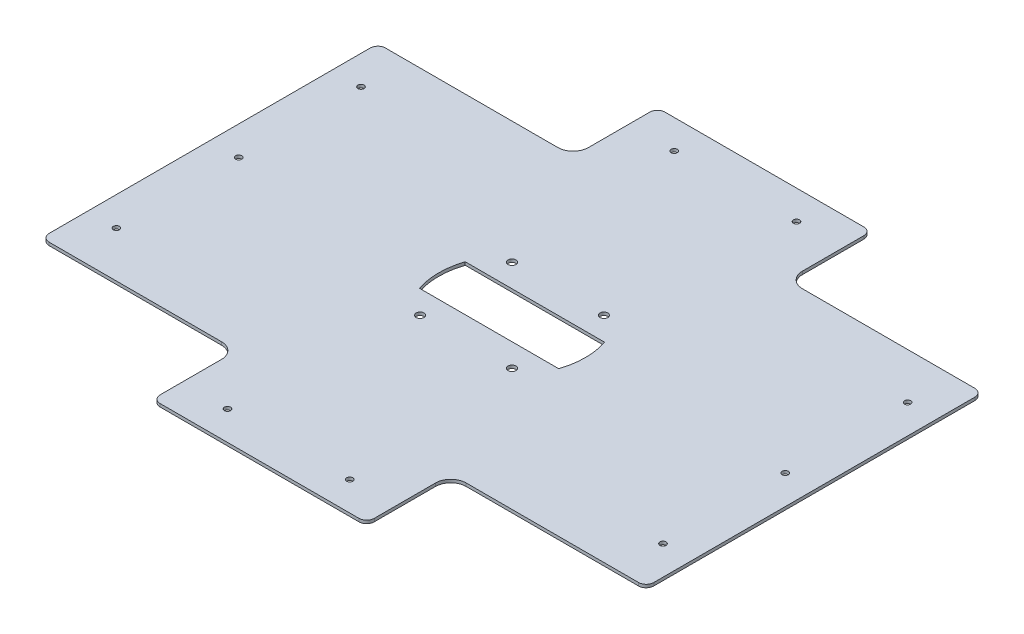
SolidWorks part; units mm, degrees
material "1060 Сплав"
ref_plane "Спереди" through (0, 0, 0) normal (0, 0, 1) x (1, 0, 0)
ref_plane "Сверху" through (0, 0, 0) normal (0, 1, 0) x (1, 0, 0)
ref_plane "Справа" through (0, 0, 0) normal (1, 0, 0) x (0, 0, -1)
sketch "Эскиз1" plane through (0, 0, 0) normal (0, 1, 0) x (1, 0, 0)
  line L1 (-65, -165.1043) -> (65, -165.1043)
  line L2 (-197.7687, -105) -> (-197.7687, 105)
  line L3 (-65, 165.1043) -> (65, 165.1043)
  line L4 (197.7687, -105) -> (197.7687, 105)
  line L18 (-284.5497, 0) -> (284.3305, 0) construction
  line L39 (-70, 120) -> (-70, 160.1043)
  line L40 (0, 262.7398) -> (0, -186.5795) construction
  line L41 (-192.7687, 110) -> (-80, 110)
  line L43 (-192.7687, -110) -> (-80, -110)
  line L44 (-70, -120) -> (-70, -160.1043)
  line L45 (70, 120) -> (70, 160.1043)
  line L46 (192.7687, 110) -> (80, 110)
  line L47 (192.7687, -110) -> (80, -110)
  line L48 (70, -120) -> (70, -160.1043)
  line L54 (160.9018, -110) -> (134.9018, -110)
  line L60 (160.9018, 110) -> (134.9018, 110)
  arc A0 (70, -120) -> (80, -110) centre (80, -120) cw
  arc A1 (70, 120) -> (80, 110) centre (80, 120) ccw
  arc A2 (-80, -110) -> (-70, -120) centre (-80, -120) cw
  arc A3 (-70, 120) -> (-80, 110) centre (-80, 120) cw
  arc A4 (192.7687, -110) -> (197.7687, -105) centre (192.7687, -105) ccw
  arc A5 (70, -160.1043) -> (65, -165.1043) centre (65, -160.1043) cw
  arc A6 (-70, -160.1043) -> (-65, -165.1043) centre (-65, -160.1043) ccw
  arc A7 (-192.7687, -110) -> (-197.7687, -105) centre (-192.7687, -105) cw
  arc A8 (-192.7687, 110) -> (-197.7687, 105) centre (-192.7687, 105) ccw
  arc A9 (197.7687, 105) -> (192.7687, 110) centre (192.7687, 105) ccw
  arc A10 (70, 160.1043) -> (65, 165.1043) centre (65, 160.1043) ccw
  arc A11 (-70, 160.1043) -> (-65, 165.1043) centre (-65, 160.1043) cw
  circle A22 centre (178.7687, 0) radius 2
  circle A23 centre (178.7687, 80) radius 2
  circle A24 centre (178.7687, -80) radius 2
  circle A25 centre (-178.7687, -80) radius 2
  circle A26 centre (-178.7687, 0) radius 2
  circle A27 centre (-178.7687, 80) radius 2
  circle A28 centre (40, 146.1043) radius 2
  circle A29 centre (-40, 146.1043) radius 2
  circle A30 centre (-40, -146.1043) radius 2
  circle A31 centre (40, -146.1043) radius 2
  point P0 (0, 0)
  point P3 (70, -110)
  point P8 (197.7687, 0)
  point P18 (-147.9018, 110)
  point P46 (70, 110)
  point P52 (-70, -110)
  point P55 (-70, 110)
  point P56 (-147.9018, 0)
  point P77 (197.7687, -110)
  point P80 (70, -165.1043)
  point P83 (-70, -165.1043)
  point P86 (-197.7687, -110)
  point P89 (-197.7687, 110)
  point P92 (197.7687, 110)
  point P95 (70, 165.1043)
  point P98 (-70, 165.1043)
  dimension "D2" = 4
  dimension "D6" = 10
  dimension "D11" = 40
  dimension "D12" = 330.2086
  dimension "D4" = 5
  dimension "D1" = 4
  dimension "D8" = 4
  dimension "D3" = 19
  dimension "D5" = 80
  dimension "D7" = 19
  dimension "D9" = 140
  dimension "D10" = 19
  dimension "D13" = 395.5373
sketch "Эскиз2" plane through (0, 0, 0) normal (0, 1, 0) x (1, 0, 0)
  line L0 (-162.9105, 114) -> (-136.9105, 114)
  line L1 (-162.9105, 114) -> (-162.9105, 0)
  line L2 (-162.9105, 0) -> (-136.9105, 0)
  line L3 (-136.9105, 114) -> (-136.9105, 0)
  line L4 (-149.9105, -192.6295) -> (-149.9105, 209.9923) construction
  line L5 (-162.9105, 0) -> (-136.9105, 0)
  line L6 (-162.9105, 0) -> (-162.9105, -114)
  line L7 (-162.9105, -114) -> (-136.9105, -114)
  line L8 (-136.9105, 0) -> (-136.9105, -114)
  line L9 (-99.9105, -123.5568) -> (-199.9105, -123.5568)
  line L10 (-99.9105, 163.4996) -> (-199.9105, 163.4996)
  line L11 (-99.9105, 163.4996) -> (-99.9105, 123.4996)
  line L12 (-99.9105, 123.4996) -> (-199.9105, 123.4996)
  line L13 (-199.9105, 163.4996) -> (-199.9105, 123.4996)
  line L14 (-199.9105, -163.5568) -> (-199.9105, -123.5568)
  line L15 (-99.9105, -163.5568) -> (-199.9105, -163.5568)
  line L16 (-99.9105, -163.5568) -> (-99.9105, -123.5568)
  line L17 (-284.5497, 0) -> (284.3305, 0) construction
  point P11 (-149.9105, 0)
  point P12 (-149.9105, 0)
sketch "Эскиз3" plane through (0, 0, 0) normal (0, 1, 0) x (1, 0, 0)
  line L0 (-89.8176, -177.9027) -> (70.2405, -177.9027)
  line L1 (-209.7886, -106.9112) -> (-209.7886, 106.8353)
  line L2 (-80.029, 172.0973) -> (50.2405, 172.0973)
  line L3 (170.2114, -106.9112) -> (170.2114, 103.9123)
  line L4 (-87.1938, 124.0033) -> (-87.1938, 164.9326)
  line L5 (-202.6239, 114) -> (-97.1971, 114)
  line L6 (-202.6239, -114.076) -> (-106.9857, -114.076)
  line L7 (-96.9823, -124.0793) -> (-96.9823, -170.738)
  line L8 (57.4052, 121.0803) -> (57.4052, 164.9326)
  line L9 (163.0467, 111.077) -> (67.4085, 111.077)
  line L10 (163.0467, -114.076) -> (87.4085, -114.076)
  line L11 (77.4052, -124.0793) -> (77.4052, -170.738)
  line L13 (-162.9105, 114) -> (-136.9105, 114) construction
  arc A0 (77.4052, -124.0793) -> (87.4085, -114.076) centre (87.4085, -124.0793) cw
  arc A1 (57.4052, 121.0803) -> (67.4085, 111.077) centre (67.4085, 121.0803) ccw
  arc A2 (-106.9857, -114.076) -> (-96.9823, -124.0793) centre (-106.9857, -124.0793) cw
  arc A3 (-87.1938, 124.0033) -> (-97.1971, 114) centre (-97.1971, 124.0033) cw
  arc A4 (-80.029, 172.0973) -> (-87.1938, 164.9326) centre (-80.029, 164.9326) ccw
  arc A5 (50.2405, 172.0973) -> (57.4052, 164.9326) centre (50.2405, 164.9326) cw
  arc A6 (170.2114, 103.9123) -> (163.0467, 111.077) centre (163.0467, 103.9123) ccw
  arc A7 (170.2114, -106.9112) -> (163.0467, -114.076) centre (163.0467, -106.9112) cw
  arc A8 (70.2405, -177.9027) -> (77.4052, -170.738) centre (70.2405, -170.738) ccw
  arc A9 (-89.8176, -177.9027) -> (-96.9823, -170.738) centre (-89.8176, -170.738) cw
  arc A10 (-209.7886, -106.9112) -> (-202.6239, -114.076) centre (-202.6239, -106.9112) ccw
  arc A11 (-209.7886, 106.8353) -> (-202.6239, 114) centre (-202.6239, 106.8353) cw
  point P36 (115.2276, 111.077)
  point P39 (-149.9105, 114)
  point P42 (-149.9105, 114)
  dimension "D3" = 10.0033
  dimension "D4" = 7.1647
  dimension "D1" = 380
  dimension "D2" = 350
  dimension "D5" = 112.8062
  dimension "D6" = 63.8267
  dimension "D7" = 61.0203
extrude "Бобышка-Вытянуть1" add sketch "Эскиз1" along normal blind 2 separate body
sketch "Эскиз5" plane through (0, 0, 0) normal (0, -1, 0) x (1, 0, 0)
  line L0 (45.5961, -15) -> (-45.5961, -15)
  line L5 (48, 0) -> (0, 0) construction
  line L7 (45.5961, 15) -> (-45.5961, 15)
  arc A2 (-45.5961, 15) -> (-45.5961, -15) centre (0, 0) ccw
  arc A3 (45.5961, -15) -> (45.5961, 15) centre (0, 0) ccw
  point P0 (0, 0)
  dimension "D2" = 15
  dimension "D1" = 30
  dimension "D4" = 96
extrude "Вырез-Вытянуть2" cut sketch "Эскиз5" against normal through all
hole_wizard "Сверло под метчик  спиральное M51" positions "Эскиз6" profile "Эскиз7" hole size "M5x0.8" standard "DIN"
sketch "Эскиз6" plane through (0, 2, 0) normal (0, 1, 0) x (1, 0, 0)
  line L0 (0, 0) -> (0, 24.7801) construction
  line L1 (30.052, 30.052) -> (0, 0) construction
  circle A0 centre (0, 0) radius 42.5
  point P15 (30.052, 30.052)
  dimension "D1" = 85
  dimension "D2" = 45
sketch "Эскиз7" plane through (30.052, 2, -30.052) normal (1, 0, 0) x (0, 0, 1)
  line L0 (0, 0) -> (0, 9.5622)
  line L1 (0, 9.5622) -> (2.6, 8)
  line L2 (2.6, 8) -> (2.6, 0)
  line L5 (2.6, 0) -> (0, 0)
  line L10 (0, 9.5622) -> (-2.6, 8) construction
  line L11 (0, -6.35) -> (0, 107.95) construction
  dimension "Диаметр отверстия" = 5.2
  dimension "Глубина отверстия" = 8
  dimension "Угол заточки сверла" = 118
pattern_circular "Круговой массив1" count 4 over 360 about axis through (0, 0, 0) along (0, 1, 0) of "Сверло под метчик  спиральное M51"
